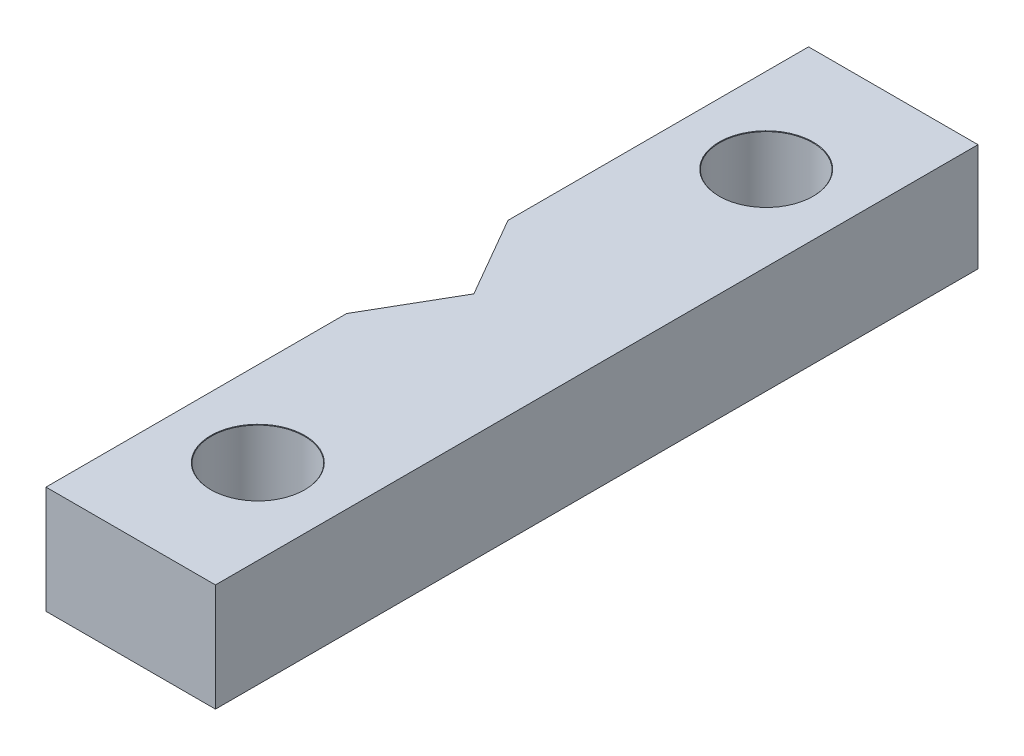
SolidWorks part; units mm, degrees
material "Plain Carbon Steel"
ref_plane "Front Plane" through (0, 0, 0) normal (0, 0, 1) x (1, 0, 0)
ref_plane "Top Plane" through (0, 0, 0) normal (0, 1, 0) x (1, 0, 0)
ref_plane "Right Plane" through (0, 0, 0) normal (1, 0, 0) x (0, 0, -1)
sketch "Sketch1" plane through (0, 0, 0) normal (0, 1, 0) x (1, 0, 0)
  line L0 (0.7494, 22.5) -> (10.7494, 22.5)
  line L1 (1.7494, 3.03) -> (-1.7494, 3.03)
  line L2 (-1.7494, 3.03) -> (-3.4987, 0)
  line L3 (-3.4987, 0) -> (-1.7494, -3.03)
  line L4 (-1.7494, -3.03) -> (1.7494, -3.03)
  line L5 (1.7494, -3.03) -> (3.4987, 0)
  line L6 (3.4987, 0) -> (1.7494, 3.03)
  line L13 (10.7494, 22.5) -> (10.7494, 7.5)
  line L15 (3.4987, 0) -> (10.7494, 0)
  line L16 (0.7494, -22.5) -> (10.7494, -22.5)
  line L17 (10.7494, -22.5) -> (10.7494, -7.5)
  line L18 (0.7494, -22.5) -> (0.7494, -4.7621)
  line L19 (0.7494, 4.7621) -> (0.7494, 22.5)
  line L22 (1.7494, 3.03) -> (0.7494, 4.7621)
  line L23 (1.7494, -3.03) -> (0.7494, -4.7621)
  line L24 (10.7494, 7.5) -> (10.7494, -7.5)
  circle A0 centre (0, 0) radius 3.03 construction
  dimension "D1" = 6.06
  dimension "D2" = 6.9975
  dimension "D3" = 10
  dimension "D4" = 15
extrude "Boss-Extrude1" add sketch "Sketch1" along normal blind 6.35
hole_wizard "M5 Clearance Hole1" positions "Sketch4" profile "Sketch3" hole size "M5" standard "ANSI Metric"
sketch "Sketch4" plane through (10.7494, 0, 0) normal (1, 0, 0) x (0, 0, -1)
  line L0 (-22.5, 0) -> (22.5, 0) construction
  line L1 (-22.5, 6.35) -> (-22.5, 0) construction
  line L2 (22.5, 6.35) -> (22.5, 0) construction
  point P0 (-15, 5)
  point P2 (15, 5)
  dimension "D1" = 5
  dimension "D2" = 7.5
  dimension "D3" = 7.5
sketch "Sketch3" plane through (10.7494, 5, 15) normal (0, 1, 0) x (0, 0, -1)
  line L0 (0, 0) -> (0, 11.7524)
  line L1 (0, 11.7524) -> (2.75, 10.1)
  line L2 (2.75, 10.1) -> (2.75, 0.025)
  line L3 (2.75, 0.025) -> (2.775, 0)
  line L5 (2.775, 0) -> (0, 0)
  line L6 (-2.75, 0.025) -> (-2.775, 0) construction
  line L10 (0, 11.7524) -> (-2.75, 10.1) construction
  line L11 (0, -6.35) -> (0, 107.95) construction
  dimension "Hole Dia." = 5.5
  dimension "Hole Depth" = 10.1
  dimension "Near C'Sink Dia." = 5.55
  dimension "Near C'Sink Angle" = 90
  dimension "Drill Angle" = 118
hole_wizard "M5 Clearance Hole2" positions "Sketch7" profile "Sketch6" hole size "M5" standard "ANSI Metric"
sketch "Sketch7" plane through (0, 6.35, 0) normal (0, 1, 0) x (1, 0, 0)
  line L2 (0.7494, 22.5) -> (10.7494, 22.5) construction
  line L3 (0.7494, -22.5) -> (10.7494, -22.5) construction
  line L4 (10.7494, 22.5) -> (10.7494, -22.5) construction
  point P7 (5.7494, 15)
  point P9 (5.7494, -15)
  dimension "D1" = 5
  dimension "D3" = 7.5
  dimension "D4" = 7.5
sketch "Sketch6" plane through (5.7494, 6.35, -15) normal (1, 0, 0) x (0, 0, 1)
  line L0 (0, 0) -> (0, 11.7524)
  line L1 (0, 11.7524) -> (2.75, 10.1)
  line L2 (2.75, 10.1) -> (2.75, 0.025)
  line L3 (2.75, 0.025) -> (2.775, 0)
  line L5 (2.775, 0) -> (0, 0)
  line L6 (-2.75, 0.025) -> (-2.775, 0) construction
  line L10 (0, 11.7524) -> (-2.75, 10.1) construction
  line L11 (0, -6.35) -> (0, 107.95) construction
  dimension "Hole Dia." = 5.5
  dimension "Hole Depth" = 10.1
  dimension "Near C'Sink Dia." = 5.55
  dimension "Near C'Sink Angle" = 90
  dimension "Drill Angle" = 118
